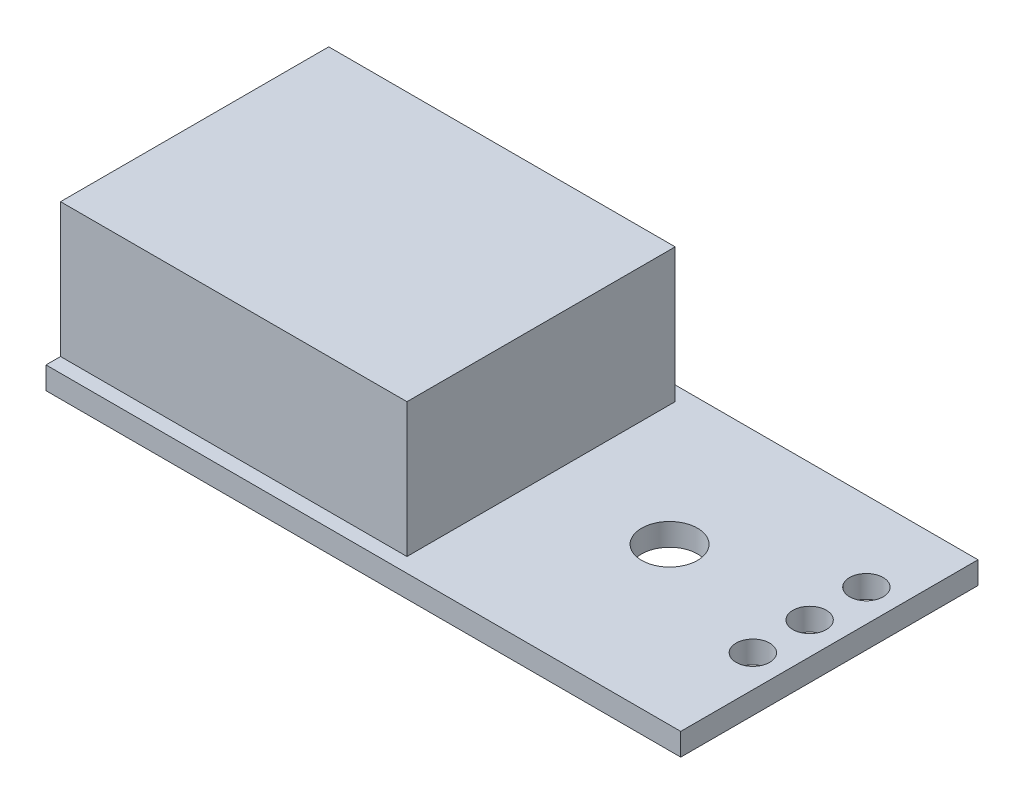
SolidWorks part; units mm, degrees
ref_plane "前视基准面" through (0, 0, 0) normal (0, 0, 1) x (1, 0, 0)
ref_plane "上视基准面" through (0, 0, 0) normal (0, 1, 0) x (1, 0, 0)
ref_plane "右视基准面" through (0, 0, 0) normal (1, 0, 0) x (0, 0, -1)
sketch "草图1" plane through (0, 0, 0) normal (0, 1, 0) x (1, 0, 0)
  line L1 (-14.2, 6.65) -> (14.2, 6.65)
  line L2 (-14.2, 6.65) -> (-14.2, -6.65)
  line L3 (-14.2, -6.65) -> (14.2, -6.65)
  line L4 (14.2, 6.65) -> (14.2, -6.65)
  line L5 (-14.2, 6.65) -> (14.2, -6.65) construction
  line L6 (-14.2, -6.65) -> (14.2, 6.65) construction
  point P0 (0, 0)
  dimension "D1" = 28.4
  dimension "D2" = 13.3
extrude "凸台-拉伸1" add sketch "草图1" along normal blind 1
sketch "草图2" plane through (0, 1, 0) normal (0, 1, 0) x (1, 0, 0)
  line L1 (-14.2, -6.65) -> (14.2, -6.65) construction
  line L2 (14.2, -6.65) -> (14.2, 6.65) construction
  circle A0 centre (6.7, 0.35) radius 1.25
  dimension "D1" = 2.5
  dimension "D2" = 7
  dimension "D3" = 7.5
extrude "切除-拉伸1" cut sketch "草图2" against normal through all
sketch "草图3" plane through (0, 1, 0) normal (0, 1, 0) x (1, 0, 0)
  line L0 (-14.2, 6.65) -> (-14.2, -6.65) construction
  line L1 (-14.2, 6) -> (1.3, 6)
  line L2 (-14.2, 6) -> (-14.2, -6)
  line L3 (-14.2, -6) -> (1.3, -6)
  line L4 (1.3, 6) -> (1.3, -6)
  line L5 (0, 0) -> (-14.2, 0) construction
  dimension "D1" = 15.5
  dimension "D2" = 12
extrude "凸台-拉伸2" add sketch "草图3" along normal blind 7 from surface at -1 starting at face at (6.7, 0, 0.9)
sketch "草图4" plane through (0, 1, 0) normal (0, 1, 0) x (1, 0, 0)
  circle A0 centre (12.7653, 3.0913) radius 0.75
  dimension "D1" = 1.5
extrude "切除-拉伸2" cut sketch "草图4" against normal through all
pattern_linear "阵列(线性)1" count 3 spacing 2.54 along (0, 0, 1) of "切除-拉伸2"
